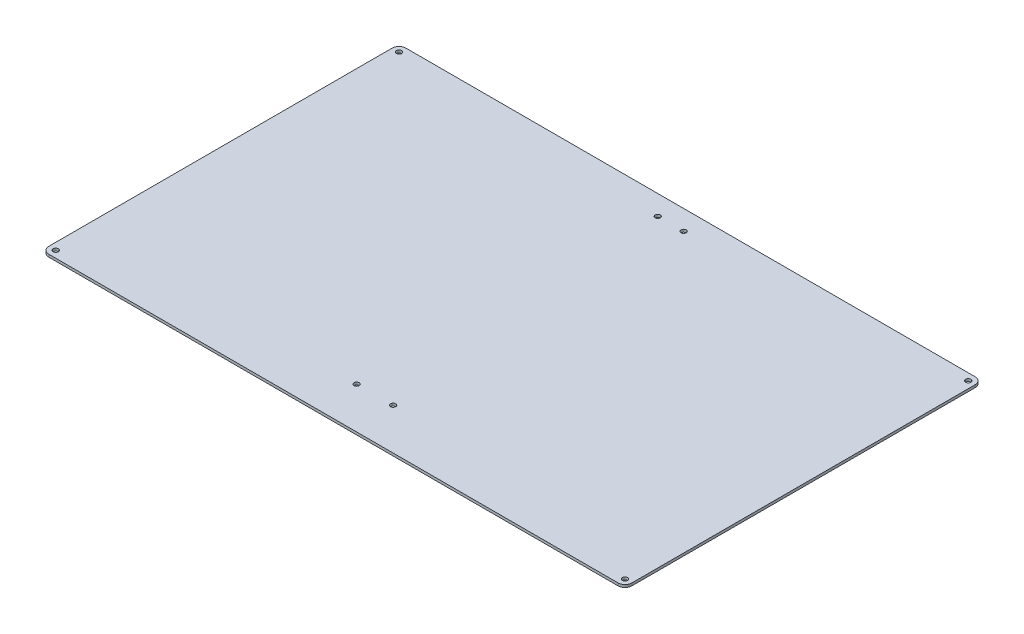
SolidWorks part; units mm, degrees
material "Hexcel AS4C (3000 Filaments)"
ref_plane "Front Plane" through (0, 0, 0) normal (0, 0, 1) x (1, 0, 0)
ref_plane "Top Plane" through (0, 0, 0) normal (0, 1, 0) x (1, 0, 0)
ref_plane "Right Plane" through (0, 0, 0) normal (1, 0, 0) x (0, 0, -1)
sketch "Sketch1" plane through (0, 0, 0) normal (0, 1, 0) x (1, 0, 0)
  line L0 (-169, 103.5) -> (169, 103.5)
  line L1 (-170, 104.5) -> (170, 104.5) construction
  line L2 (-170, 104.5) -> (-170, -104.5) construction
  line L3 (-170, -104.5) -> (170, -104.5) construction
  line L4 (170, 104.5) -> (170, -104.5) construction
  line L5 (-170, 104.5) -> (170, -104.5) construction
  line L6 (-170, -104.5) -> (170, 104.5) construction
  line L7 (169, 103.5) -> (169, -103.5)
  line L8 (-169, -103.5) -> (169, -103.5)
  line L9 (-169, 103.5) -> (-169, -103.5)
  point P0 (0, 0)
  dimension "D1" = 209
  dimension "D2" = 340
  dimension "D3" = 1
extrude "Boss-Extrude1" add sketch "Sketch1" along normal blind 1.5
fillet "Fillet1" radius 4 4 edges at (-169, 0.75, -103.5) (-169, 0.75, 103.5) (169, 0.75, 103.5) (169, 0.75, -103.5)
hole_wizard "Ø3.0mm Dowel Hole1" positions "Sketch3" profile "Sketch2" hole size "Ø3.0" standard "ISO"
sketch "Sketch3" plane through (0, 1.5, 0) normal (0, 1, 0) x (1, 0, 0)
  arc A0 (165, -103.5) -> (169, -99.5) centre (165, -99.5) ccw construction
  arc A1 (169, 99.5) -> (165, 103.5) centre (165, 99.5) ccw construction
  arc A2 (-165, 103.5) -> (-169, 99.5) centre (-165, 99.5) ccw construction
  arc A3 (-169, -99.5) -> (-165, -103.5) centre (-165, -99.5) ccw construction
  point P0 (-165, -99.5)
  point P3 (-165, 99.5)
  point P5 (165, 99.5)
  point P7 (165, -99.5)
  point P25 (-10.5779, -79.5)
  point P28 (10.5779, -79.5)
  point P31 (-7.5, 92)
  point P34 (7.5, 92)
sketch "Sketch2" plane through (-165, 1.5, 99.5) normal (1, 0, 0) x (0, 0, 1)
  line L0 (0, 0) -> (0, 18.1913)
  line L1 (0, 18.1913) -> (1.5, 17.29)
  line L2 (1.5, 17.29) -> (1.5, 0)
  line L5 (1.5, 0) -> (0, 0)
  line L10 (0, 18.1913) -> (-1.5, 17.29) construction
  line L11 (0, -6.35) -> (0, 107.95) construction
  dimension "Hole Dia." = 3
  dimension "Hole Depth" = 17.29
  dimension "Drill Angle" = 118
